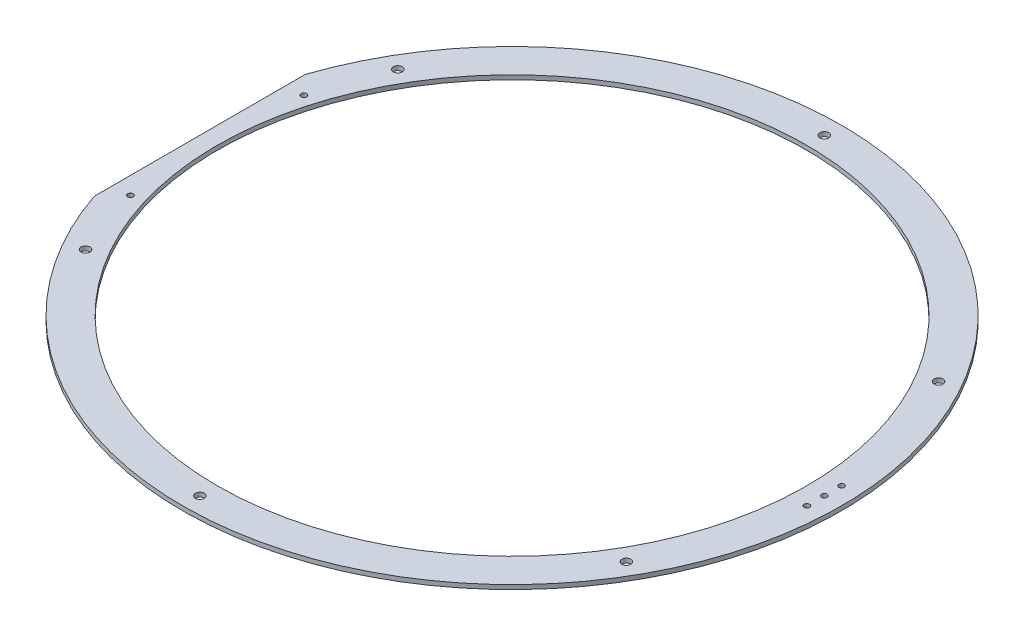
SolidWorks part; units mm, degrees
material "PC High Viscosity"
ref_plane "Front Plane" through (0, 0, 0) normal (0, 0, 1) x (1, 0, 0)
ref_plane "Top Plane" through (0, 0, 0) normal (0, 1, 0) x (1, 0, 0)
ref_plane "Right Plane" through (0, 0, 0) normal (1, 0, 0) x (0, 0, -1)
sketch "Sketch1" plane through (0, 0, 0) normal (0, 1, 0) x (1, 0, 0)
  line L0 (0, 215.9) -> (0, -215.9) construction
  line L1 (-228.6, 77.2511) -> (-228.6, -77.2511)
  line L2 (381, 101.6) -> (381, -101.6)
  line L3 (381, 101.6) -> (330.2, 101.6)
  line L4 (381, -101.6) -> (330.2, -101.6)
  line L5 (330.2, -101.6) -> (330.2, 101.6)
  line L6 (-228.6, 77.2511) -> (-279.4, 77.2511)
  line L7 (-279.4, 77.2511) -> (-279.4, -77.2511)
  line L8 (-279.4, -77.2511) -> (-228.6, -77.2511)
  line L9 (241.3, 0) -> (-241.3, 0) construction
  circle A0 centre (0, 0) radius 241.3
  circle A1 centre (0, 0) radius 215.9
  circle A2 centre (0, 228.6) radius 3.2639
  circle A3 centre (197.9734, 114.3) radius 3.2639
  circle A4 centre (197.9734, -114.3) radius 3.2639
  circle A5 centre (0, -228.6) radius 3.2639
  circle A6 centre (-197.9734, -114.3) radius 3.2639
  circle A7 centre (-197.9734, 114.3) radius 3.2639
  circle A13 centre (228.6, 0) radius 2.0193
  circle A14 centre (228.6, -12.7) radius 2.0193
  circle A15 centre (228.6, 12.7) radius 2.0193
  circle A16 centre (-215.9, 63.5) radius 2.0193
  circle A17 centre (-215.9, -63.5) radius 2.0193
  point P19 (0, 0)
  point P21 (0, 0)
  point P31 (381, 0)
  point P32 (-228.6, 0)
  point P40 (0, 0)
  dimension "D1" = 482.6
  dimension "D2" = 431.8
  dimension "D3" = 6.5278
  dimension "D7" = 63.5
  dimension "D8" = 0
  dimension "D6" = 215.9
  dimension "D10" = 4.0386
  dimension "D11" = 4.0386
  dimension "D13" = 4.0386
  dimension "D18" = 4.0386
  dimension "D19" = 4.0386
  dimension "D4" = 228.6
  dimension "D9" = 228.6
  dimension "front_distance" = 228.6
  dimension "D12" = 50.8
  dimension "distance_from_center" = 381
  dimension "cut_width" = 203.2
  dimension "D14" = 0
  dimension "D15" = 50.8
  dimension "cut_size" = 154.5022
  dimension "D16" = 12.7
  dimension "D17" = 12.7
  dimension "D20" = 63.5
  dimension "D5" = 6
extrude "Boss-Extrude1" add sketch "Sketch1" along normal blind 3.175
